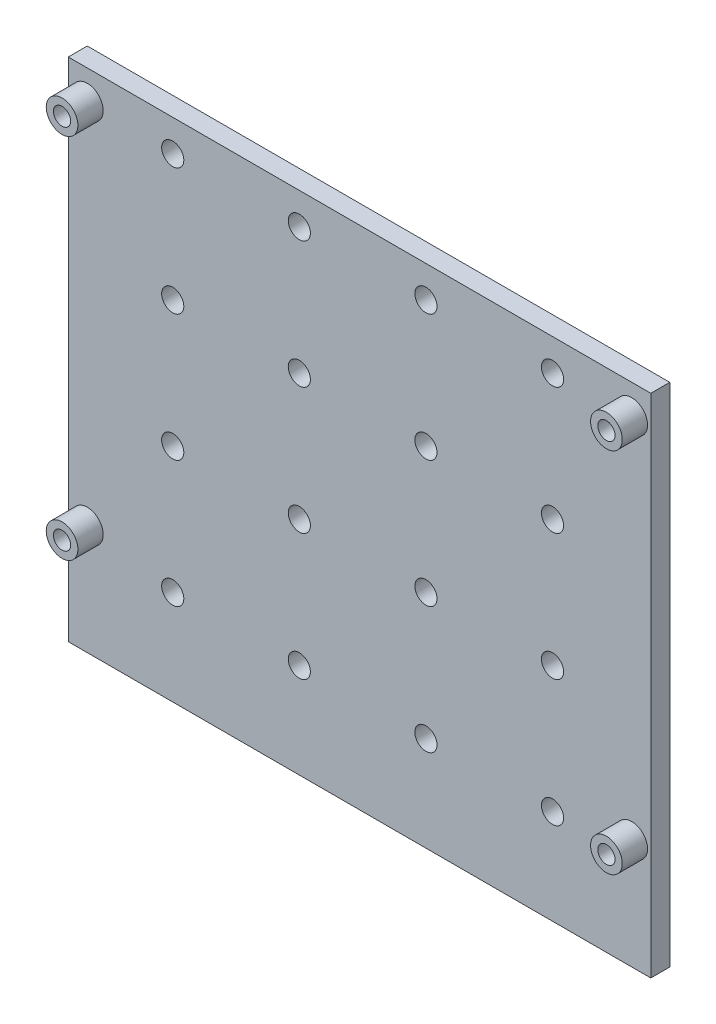
SolidWorks part; units mm, degrees
ref_plane "Front Plane" through (0, 0, 0) normal (0, 0, 1) x (1, 0, 0)
ref_plane "Top Plane" through (0, 0, 0) normal (0, 1, 0) x (1, 0, 0)
ref_plane "Right Plane" through (0, 0, 0) normal (1, 0, 0) x (0, 0, -1)
sketch "Sketch1" plane through (0, 0, 0) normal (0, 0, 1) x (1, 0, 0)
  line L0 (-43.1111, 35.4) -> (35.9093, 35.4) construction
  line L1 (-46.0125, -40) -> (46.0125, -40)
  line L2 (-46.0125, -40) -> (-46.0125, 40)
  line L3 (-46.0125, 40) -> (46.0125, 40)
  line L4 (46.0125, -40) -> (46.0125, 40)
  line L5 (-46.0125, -40) -> (46.0125, 40) construction
  line L6 (-46.0125, 40) -> (46.0125, -40) construction
  circle A0 centre (-42.9975, 35.4) radius 1.365
  circle A1 centre (43.0025, 35.4) radius 1.365
  circle A2 centre (-42.9975, -22.6) radius 1.365
  circle A3 centre (43.0025, -22.6) radius 1.365
  point P0 (0, 0)
  point P14 (0, 0)
  point P15 (0, 0)
  dimension "D4" = 2.73
  dimension "D1" = 3.01
  dimension "D2" = 80
  dimension "D3" = 5.5
  dimension "D5" = 4.6
  dimension "D6" = 86
  dimension "D7" = 58
extrude "Boss-Extrude1" add sketch "Sketch1" along normal blind 3
sketch "Sketch2" plane through (0, 0, 3) normal (0, 0, 1) x (1, 0, 0)
  line L1 (-39.9975, 32.6163) -> (40.0025, 32.6163)
  line L2 (-39.9975, 32.6163) -> (-39.9975, -32.6163)
  line L3 (-39.9975, -32.6163) -> (40.0025, -32.6163)
  line L4 (40.0025, 32.6163) -> (40.0025, -32.6163)
  line L7 (-72.6262, 0) -> (-68.3619, 0) construction
  line L8 (0, 19.3692) -> (0, -5.0844) construction
  line L9 (46.0125, 40) -> (-46.0125, 40) construction
  line L10 (-46.0125, 40) -> (-46.0125, -40) construction
  circle A0 centre (-42.9975, 35.4) radius 1.365 construction
  circle A1 centre (43.0025, 35.4) radius 1.365 construction
  point P0 (0, 0)
  point P11 (36.0222, 32.6102)
  point P12 (0, 40)
  point P15 (-46.0125, 0)
  dimension "D1" = 3
  dimension "D2" = 3
extrude "Cut-Extrude1" [suppressed] cut sketch "Sketch2" against normal blind 3
sketch "Sketch3" plane through (0, 0, 3) normal (0, 0, 1) x (1, 0, 0)
  circle A0 centre (-42.9975, 35.4) radius 2.5
  circle A1 centre (-42.9975, 35.4) radius 1.365 construction
  circle A2 centre (-42.9975, -22.6) radius 2.5
  circle A3 centre (43.0025, 35.4) radius 2.5
  circle A4 centre (43.0025, -22.6) radius 2.5
  circle A5 centre (-42.9975, -22.6) radius 1.365 construction
  circle A6 centre (43.0025, -22.6) radius 1.365 construction
  circle A7 centre (43.0025, 35.4) radius 1.365 construction
  circle A8 centre (-42.9975, 35.4) radius 1.365
  circle A9 centre (43.0025, -22.6) radius 1.365
  circle A10 centre (43.0025, 35.4) radius 1.365
  circle A11 centre (-42.9975, -22.6) radius 1.365
  point P24 (-11.6614, 10.6039)
  point P25 (5.2324, 23.7106)
  point P26 (-31.0771, 10.9935)
  point P27 (0, 0)
  point P28 (0, 0)
  point P29 (0, 0)
  dimension "D1" = 5
  dimension "D2" = 2.73
extrude "Boss-Extrude2" add sketch "Sketch3" along normal blind 4
sketch "Sketch4" plane through (0, 0, 3) normal (0, 0, 1) x (1, 0, 0)
  line L0 (46.0125, 40) -> (-46.0125, 40) construction
  line L1 (-46.0125, 40) -> (-46.0125, -40) construction
  circle A0 centre (-29.5125, 35) radius 1.75
  point P2 (0, 0)
  point P5 (-40.8326, 35)
  point P6 (-36.5791, 35)
  dimension "D1" = 3.5
  dimension "D2" = 5
  dimension "D3" = 16.5
extrude "Cut-Extrude2" cut sketch "Sketch4" against normal through all both and the other way through all
pattern_linear "LPattern1" count 4 spacing 20 along (1, 0, 0) count 4 spacing 20 along (0, -1, 0) of "Cut-Extrude2"
